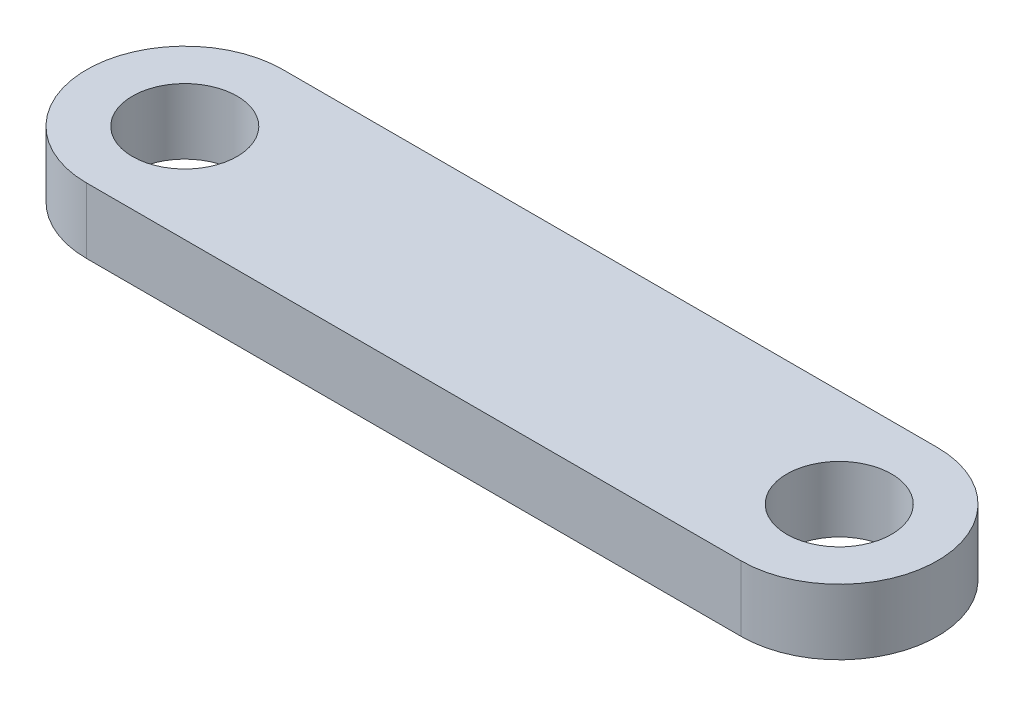
SolidWorks part; units mm, degrees
ref_plane "Front Plane" through (0, 0, 0) normal (0, 0, 1) x (1, 0, 0)
ref_plane "Top Plane" through (0, 0, 0) normal (0, 1, 0) x (1, 0, 0)
ref_plane "Right Plane" through (0, 0, 0) normal (1, 0, 0) x (0, 0, -1)
sketch "Sketch1" plane through (0, 0, 0) normal (0, 1, 0) x (1, 0, 0)
  line L0 (0, 7.5) -> (50, 7.5)
  line L1 (50, -7.5) -> (0, -7.5)
  arc A0 (0, 7.5) -> (0, -7.5) centre (0, 0) ccw
  arc A1 (50, -7.5) -> (50, 7.5) centre (50, 0) ccw
  circle A2 centre (0, 0) radius 4
  circle A3 centre (50, 0) radius 4
  dimension "D1" = 15
  dimension "D2" = 15
  dimension "D4" = 8
  dimension "D5" = 8
  dimension "D3" = 50
extrude "Boss-Extrude1" add sketch "Sketch1" along normal blind 5
